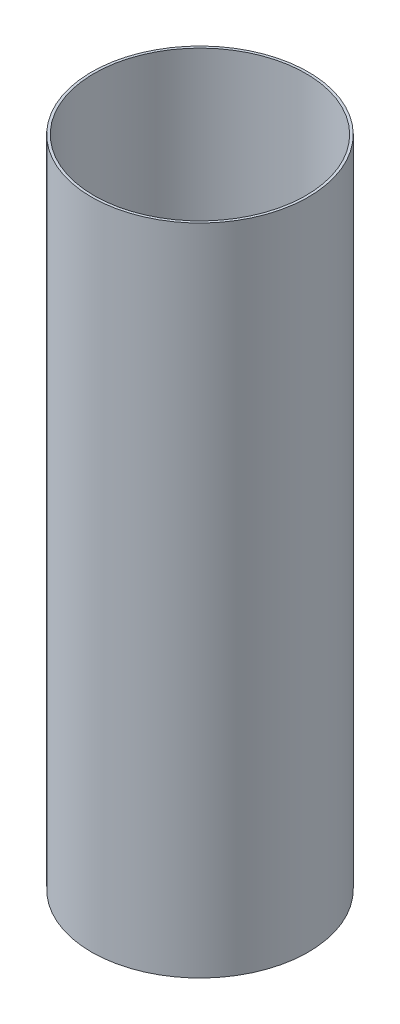
SolidWorks part; units mm, degrees
ref_plane "Front Plane" through (0, 0, 0) normal (0, 0, 1) x (1, 0, 0)
ref_plane "Top Plane" through (0, 0, 0) normal (0, 1, 0) x (1, 0, 0)
ref_plane "Right Plane" through (0, 0, 0) normal (1, 0, 0) x (0, 0, -1)
sketch "Sketch1" plane through (0, 0, 0) normal (0, 1, 0) x (1, 0, 0)
  circle A0 centre (0, 0) radius 32.385
  circle A1 centre (0, 0) radius 33.16
  dimension "D1" = 64.77
  dimension "D2" = 66.32
extrude "Boss-Extrude1" add sketch "Sketch1" along normal mid plane 200
